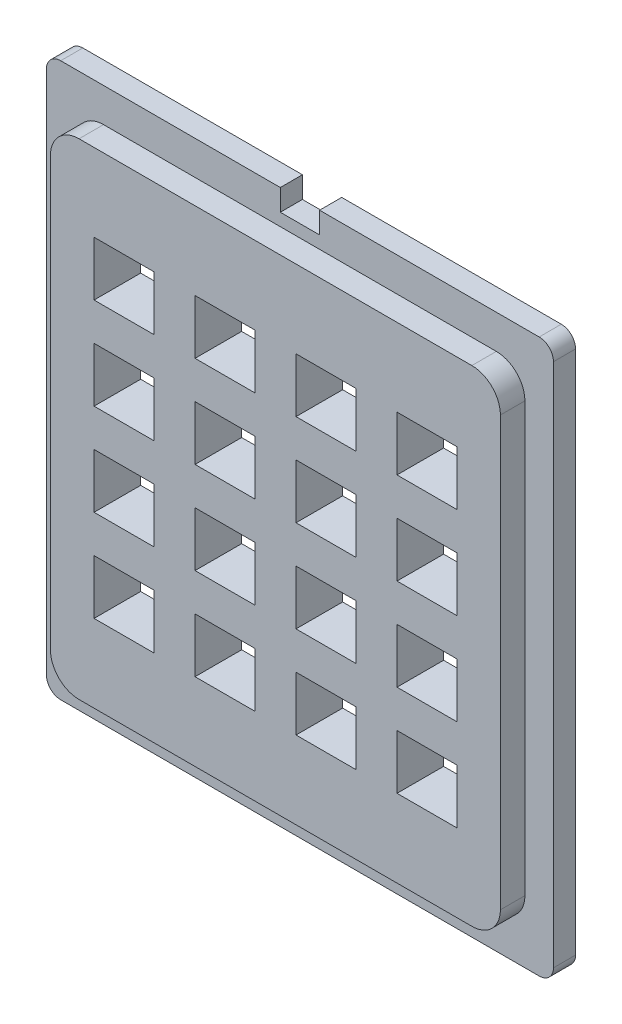
SolidWorks part; units mm, degrees
ref_plane "Front" through (0, 0, 0) normal (0, 0, 1) x (1, 0, 0)
ref_plane "Top" through (0, 0, 0) normal (0, 1, 0) x (1, 0, 0)
ref_plane "Right" through (0, 0, 0) normal (1, 0, 0) x (0, 0, -1)
sketch "Sketch1" plane through (0, 0, 0) normal (0, 0, 1) x (1, 0, 0)
  line L0 (-35.5, 0) -> (35.5, 0) construction
  line L1 (-33.5, 38.75) -> (33.5, 38.75)
  line L2 (-35.5, 36.75) -> (-35.5, -36.75)
  line L3 (-33.5, -38.75) -> (33.5, -38.75)
  line L4 (35.5, 36.75) -> (35.5, -36.75)
  line L5 (0, 35.75) -> (0, 0) construction
  line L6 (-2.75, 38.75) -> (2.75, 38.75)
  line L7 (-2.75, 38.75) -> (-2.75, 35.75)
  line L8 (-2.75, 35.75) -> (2.75, 35.75)
  line L9 (2.75, 38.75) -> (2.75, 35.75)
  arc A0 (-33.5, 38.75) -> (-35.5, 36.75) centre (-33.5, 36.75) ccw
  arc A1 (35.5, 36.75) -> (33.5, 38.75) centre (33.5, 36.75) ccw
  arc A2 (-33.5, -38.75) -> (-35.5, -36.75) centre (-33.5, -36.75) cw
  arc A3 (35.5, -36.75) -> (33.5, -38.75) centre (33.5, -36.75) cw
  point P6 (0, 0)
  point P10 (-35.5, 38.75)
  point P13 (35.5, 38.75)
  point P16 (-35.5, -38.75)
  dimension "D3" = 2
  dimension "D1" = 77.5
  dimension "D2" = 71
  dimension "D4" = 3
  dimension "D5" = 5.5
extrude "base" add sketch "Sketch1" along normal blind 3.0988 contours A3 L4 A1 L1 L9 L8 L7 A0 L2 A2 L3
sketch "Sketch4" plane through (0, 0, 3.0988) normal (0, 0, 1) x (1, 0, 0)
  line L0 (-30, 0) -> (30, 0) construction
  line L1 (-30, 29.5) -> (30, 29.5) construction
  line L2 (-30, 29.5) -> (-30, -29.5) construction
  line L3 (-30, -29.5) -> (30, -29.5) construction
  line L4 (30, 29.5) -> (30, -29.5) construction
  circle A0 centre (-30, 29.5) radius 1.016
  circle A1 centre (30, 29.5) radius 1.016
  circle A2 centre (30, -29.5) radius 1.016
  circle A3 centre (-30, -29.5) radius 1.016
  point P7 (0, 0)
  dimension "D1" = 2.032
  dimension "D2" = 59
  dimension "D3" = 60
extrude "mount holes" cut sketch "Sketch4" against normal through all
sketch "Sketch2" plane through (0, 0, 3.0988) normal (0, 0, 1) x (1, 0, 0)
  line L0 (0, 34) -> (0, -34) construction
  line L1 (-27.5, 34) -> (27.5, 34)
  line L2 (-31.5, 30) -> (-31.5, -30)
  line L3 (-27.5, -34) -> (27.5, -34)
  line L4 (31.5, 30) -> (31.5, -30)
  arc A0 (-27.5, 34) -> (-31.5, 30) centre (-27.5, 30) ccw
  arc A1 (-27.5, -34) -> (-31.5, -30) centre (-27.5, -30) cw
  arc A2 (31.5, -30) -> (27.5, -34) centre (27.5, -30) cw
  arc A3 (31.5, 30) -> (27.5, 34) centre (27.5, 30) ccw
  point P6 (0, 0)
  point P10 (-31.5, 34)
  point P13 (-31.5, -34)
  point P18 (31.5, 34)
  dimension "D3" = 4
  dimension "D1" = 63
  dimension "D2" = 68
extrude "Extrude2" add sketch "Sketch2" along normal blind 3.429
sketch "Sketch3" plane through (0, 0, 6.5278) normal (0, 0, 1) x (1, 0, 0)
  line L1 (-25.4, 23.114) -> (-17.018, 23.114)
  line L2 (-25.4, 23.114) -> (-25.4, 15.494)
  line L3 (-25.4, 15.494) -> (-17.018, 15.494)
  line L4 (-17.018, 23.114) -> (-17.018, 15.494)
  dimension "D1" = 8.382
  dimension "D2" = 7.62
  dimension "D3" = 25.4
  dimension "D4" = 23.114
extrude "key" cut sketch "Sketch3" against normal through all
pattern_linear "keys" count 4 spacing 14.1402 along (1, 0, 0) count 4 spacing 12.8694 along (0, -1, 0) of "key"
